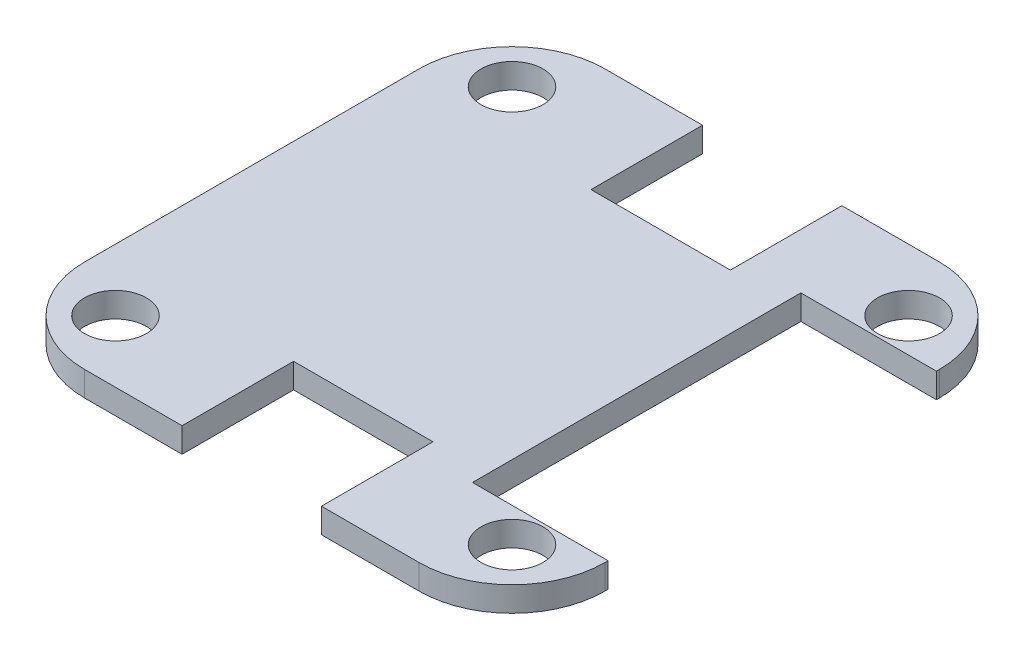
SolidWorks part; units mm, degrees
ref_plane "Front Plane" through (0, 0, 0) normal (0, 0, 1) x (1, 0, 0)
ref_plane "Top Plane" through (0, 0, 0) normal (0, 1, 0) x (1, 0, 0)
ref_plane "Right Plane" through (0, 0, 0) normal (1, 0, 0) x (0, 0, -1)
sketch "Layer1" plane through (0, 0, 0) normal (0, 1, 0) x (1, 0, 0)
  line L0 (11.25, 42) -> (27, 42)
  line L1 (-27, -42) -> (-11.25, -42)
  line L2 (-42, -27) -> (-42, 27)
  line L3 (-27, 42) -> (-11.25, 42)
  line L4 (42, -27) -> (42, 27)
  line L5 (-42, -42) -> (42, 42) construction
  line L6 (-42, 42) -> (42, -42) construction
  line L8 (-11.25, 42) -> (-11.25, 24)
  line L9 (-11.25, 24) -> (11.25, 24)
  line L10 (11.25, 42) -> (11.25, 24)
  line L12 (-11.25, -42) -> (-11.25, -24)
  line L13 (-11.25, -24) -> (11.25, -24)
  line L14 (11.25, -42) -> (11.25, -24)
  line L15 (11.25, -42) -> (27, -42)
  line L18 (-42, -21.5) -> (-42, 21.5)
  arc A0 (27, -42) -> (42, -27) centre (27, -27) ccw
  arc A1 (27, 42) -> (42, 27) centre (27, 27) cw
  arc A2 (-27, -42) -> (-42, -27) centre (-27, -27) cw
  arc A3 (-42, 27) -> (-27, 42) centre (-27, 27) cw
  point P0 (0, 0)
  point P30 (21.7219, 0)
  dimension "D9" = 15
  dimension "D1" = 84
  dimension "D2" = 84
  dimension "D3" = 18
  dimension "D4" = 22.5
  dimension "D5" = 18
  dimension "D6" = 22.5
  dimension "D7" = 30.75
  dimension "D8" = 30.75
  dimension "D10" = 43
extrude "Boss-Extrude1" add sketch "Layer1" along normal blind 4
sketch "Sketch4" plane through (0, 4, 0) normal (0, 1, 0) x (1, 0, 0)
  line L0 (11.25, 42) -> (27, 42) construction
  line L1 (20.12, -26.5) -> (42, -26.5)
  line L2 (20.12, -26.5) -> (20.12, 26.5)
  line L3 (20.12, 26.5) -> (42, 26.5)
  line L4 (42, -26.5) -> (42, 26.5)
  line L5 (20.12, -26.5) -> (42, 26.5) construction
  line L6 (20.12, 26.5) -> (42, -26.5) construction
  line L7 (42, -27) -> (42, 27) construction
  line L8 (-42, -27) -> (-42, 27) construction
  line L13 (-27, 42) -> (-11.25, 42) construction
  line L15 (-7.8, 7.8) -> (7.8, 7.8)
  line L16 (-7.8, 7.8) -> (-7.8, -12.5)
  line L17 (-7.8, -12.5) -> (7.8, -12.5)
  line L18 (7.8, 7.8) -> (7.8, -12.5)
  circle A0 centre (-32, 32) radius 5
  circle A1 centre (32, 32) radius 5
  circle A2 centre (32, -32) radius 5
  circle A3 centre (-32, -32) radius 5
  point P0 (31.06, 0)
  line M15 (42, -27) -> (42, 27)
  dimension "D9" = 10
  dimension "D1" = 53
  dimension "D2" = 21.88
  dimension "D3" = 15.5
  dimension "D4" = 0
  dimension "D10" = 10
  dimension "D11" = 10
  dimension "D5" = 20.3
  dimension "D6" = 15.6
  dimension "D7" = 34.2
  dimension "D8" = 34.2
  dimension "D12" = 2
  dimension "D13" = 2
extrude "Cut-Extrude1" cut sketch "Sketch4" against normal blind 4 contours L3 L2 L1 M15 | A1 | A0 | A3 | A2
equation "\"D6@Layer1\"=\"D4@Layer1\""
equation "\"D5@Layer1\"=\"D3@Layer1\""
equation "\"D2@Layer1\"=\"D1@Layer1\""
equation "\"D7@Layer1\"=(\"D2@Layer1\"-\"D4@Layer1\")/2"
equation "\"D8@Layer1\"=\"D7@Layer1\""
equation "\"D3@Sketch4\"=(\"D1@Layer1\"-\"D1@Sketch4\")/2"
equation "\"D11@Sketch4\"=\"D10@Sketch4\""
equation "\"D7@Sketch4\"=(\"D2@Layer1\"-\"D6@Sketch4\")/2"
equation "\"D8@Sketch4\"=(\"D1@Layer1\"-\"D6@Sketch4\")/2"
